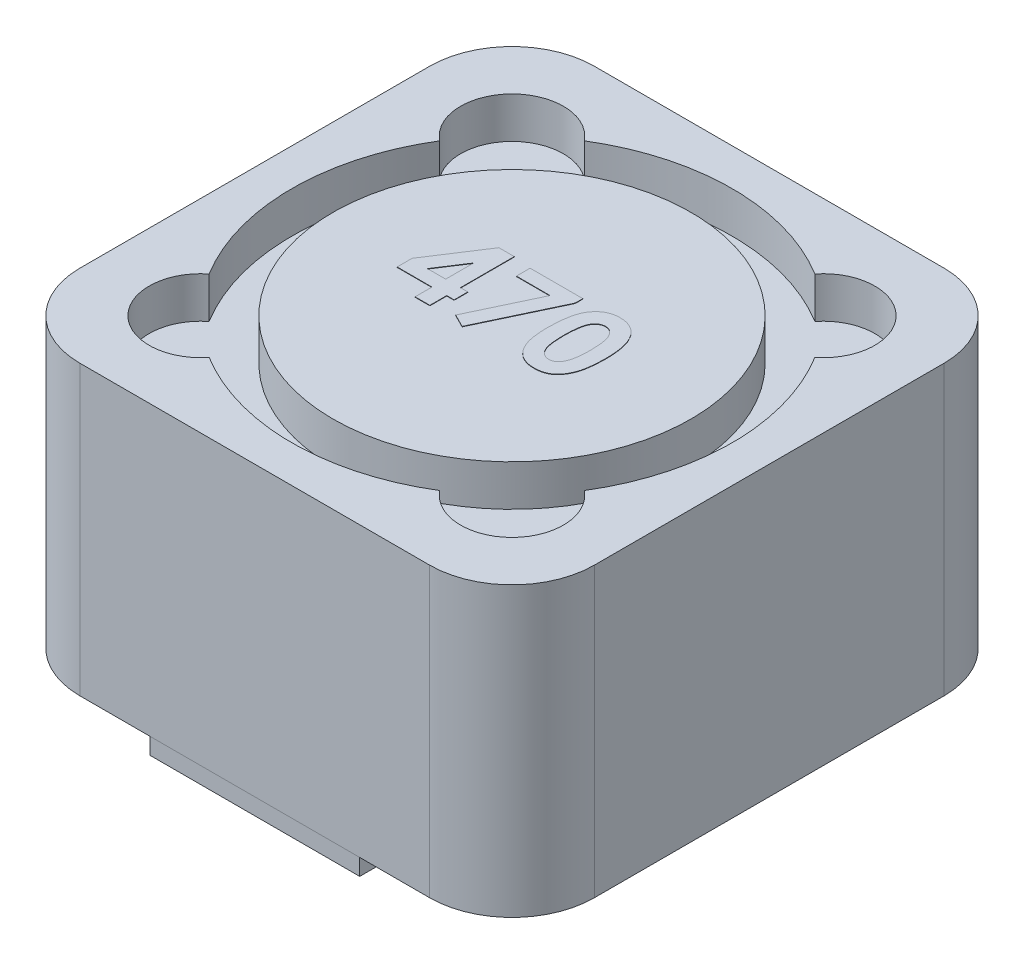
SolidWorks part; units mm, degrees
ref_plane "Front Plane" through (0, 0, 0) normal (0, 0, 1) x (1, 0, 0)
ref_plane "Top Plane" through (0, 0, 0) normal (0, 1, 0) x (1, 0, 0)
ref_plane "Right Plane" through (0, 0, 0) normal (1, 0, 0) x (0, 0, -1)
sketch "Sketch1" plane through (0, 0, 0) normal (0, 1, 0) x (1, 0, 0)
  line L1 (-6.25, -6.25) -> (6.25, -6.25)
  line L2 (-6.25, -6.25) -> (-6.25, 6.25)
  line L3 (-6.25, 6.25) -> (6.25, 6.25)
  line L4 (6.25, -6.25) -> (6.25, 6.25)
  line L5 (-6.25, -6.25) -> (6.25, 6.25) construction
  line L6 (-6.25, 6.25) -> (6.25, -6.25) construction
  point P0 (0, 0)
  dimension "D1" = 12.5
  dimension "D2" = 12.5
extrude "Boss-Extrude1" add sketch "Sketch1" along normal blind 7
sketch "Sketch2" plane through (0, 7, 0) normal (0, 1, 0) x (1, 0, 0)
  line L0 (0, 0) -> (-6.25, 6.25) construction
  line L1 (0, 0) -> (0, 2.5001) construction
  line L2 (0, 0) -> (2.6148, 0) construction
  circle A0 centre (0, 0) radius 4.35
  arc A1 (-4.5576, 2.8019) -> (-4.5576, -2.8019) centre (0, 0) ccw
  arc A2 (-2.8019, 4.5576) -> (-4.5576, 2.8019) centre (-3.783, 3.783) ccw
  arc A3 (-2.8019, -4.5576) -> (-4.5576, -2.8019) centre (-3.783, -3.783) cw
  arc A4 (2.8019, -4.5576) -> (4.5576, -2.8019) centre (3.783, -3.783) ccw
  arc A5 (2.8019, 4.5576) -> (4.5576, 2.8019) centre (3.783, 3.783) cw
  arc A6 (-2.8019, -4.5576) -> (2.8019, -4.5576) centre (0, 0) ccw
  arc A7 (4.5576, -2.8019) -> (4.5576, 2.8019) centre (0, 0) ccw
  arc A8 (2.8019, 4.5576) -> (-2.8019, 4.5576) centre (0, 0) ccw
  dimension "D1" = 2.5
  dimension "D2" = 10.7
  dimension "D3" = 8.7
extrude "Cut-Extrude1" cut sketch "Sketch2" against normal blind 1
sketch "Sketch3" plane through (0, 0, 0) normal (0, -1, 0) x (1, 0, 0)
  line L0 (-6.25, 6.25) -> (6.25, 6.25) construction
  line L1 (-2.55, 6.25) -> (2.55, 6.25)
  line L2 (-2.55, 6.25) -> (-2.55, 5.45)
  line L3 (-2.55, 5.45) -> (2.55, 5.45)
  line L4 (2.55, 6.25) -> (2.55, 5.45)
  line L5 (0, 0) -> (-1.5572, 0) construction
  line L6 (2.55, -6.25) -> (2.55, -5.45)
  line L7 (-2.55, -5.45) -> (2.55, -5.45)
  line L8 (-2.55, -6.25) -> (-2.55, -5.45)
  line L9 (-2.55, -6.25) -> (2.55, -6.25)
  point P6 (0, 5.45)
  dimension "D1" = 5.1
  dimension "D2" = 0.8
extrude "Boss-Extrude2" add sketch "Sketch3" along normal blind 0.4 separate body
sketch "Sketch4" plane through (0, 7, 0) normal (0, 1, 0) x (1, 0, 0)
  text T0 "<b>470</b>" font "Century Gothic" height 2
extrude "Boss-Extrude3" add sketch "Sketch4" along normal blind 0.01
fillet "Fillet1" radius 2 4 edges at (6.25, 3.5, -6.25) (6.25, 3.5, 6.25) (-6.25, 3.5, -6.25) (-6.25, 3.5, 6.25)
